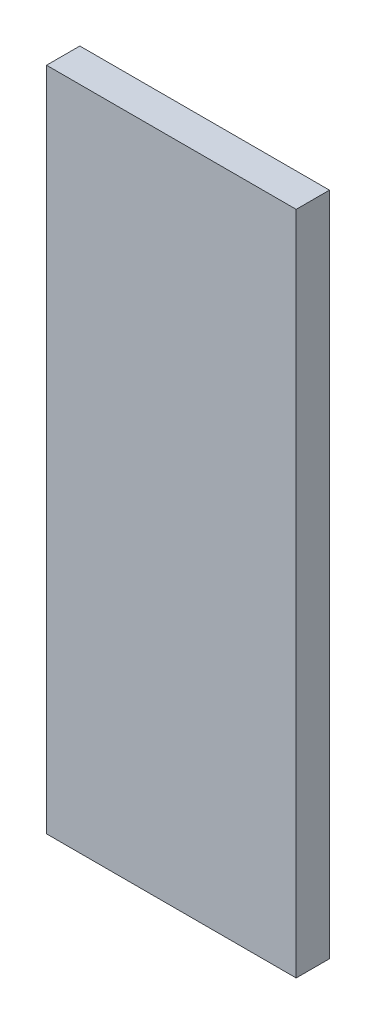
SolidWorks part; units mm, degrees
material "6061-T6 (SS)"
ref_plane "Alzado" through (0, 0, 0) normal (0, 0, 1) x (1, 0, 0)
ref_plane "Planta" through (0, 0, 0) normal (0, 1, 0) x (1, 0, 0)
ref_plane "Vista lateral" through (0, 0, 0) normal (1, 0, 0) x (0, 0, -1)
sketch "Sketch1" plane through (0, 0, 0) normal (0, 0, 1) x (1, 0, 0)
  line L1 (-15, 40) -> (15, 40)
  line L2 (-15, 40) -> (-15, -40)
  line L3 (-15, -40) -> (15, -40)
  line L4 (15, 40) -> (15, -40)
  line L5 (-15, 40) -> (15, -40) construction
  line L6 (-15, -40) -> (15, 40) construction
  point P0 (0, 0)
  dimension "D1" = 30
  dimension "D2" = 80
extrude "Boss-Extrude1" add sketch "Sketch1" along normal blind 4
sketch "Sketch2" plane through (0, 0, 4) normal (0, 0, 1) x (1, 0, 0)
  line L5 (15, 1.25) -> (0, 1.25)
  line L12 (15, -40) -> (15, 40) construction
  line L13 (0, 1.25) -> (0, -1.25)
  line L14 (0, -1.25) -> (15, -1.25)
  line L15 (15, -1.25) -> (15, 1.25)
  point P8 (0, 0)
  dimension "D1" = 2.5
extrude "Cut-Extrude1" [suppressed] cut sketch "Sketch2" against normal blind 10
fillet "Fillet1" [suppressed] radius 2
